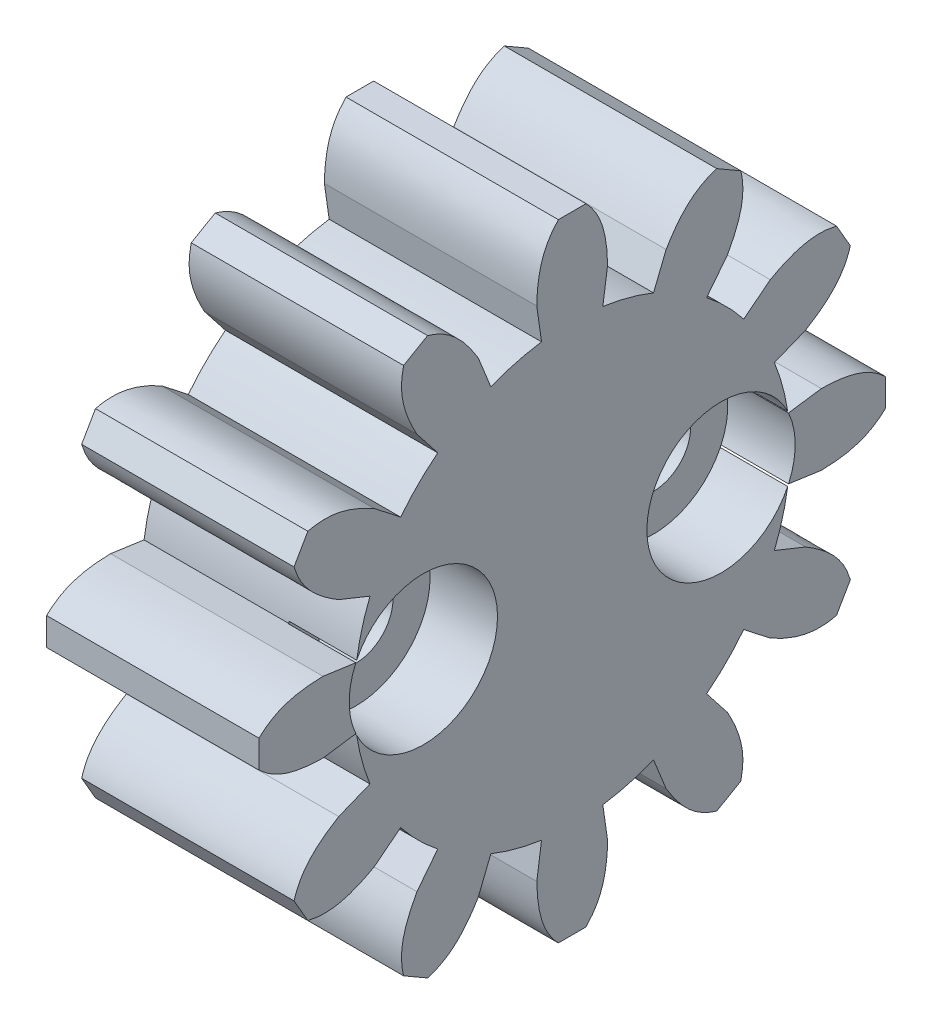
SolidWorks part; units mm, degrees
ref_plane "Front Plane" through (0, 0, 0) normal (0, 0, 1) x (1, 0, 0)
ref_plane "Top Plane" through (0, 0, 0) normal (0, 1, 0) x (1, 0, 0)
ref_plane "Right Plane" through (0, 0, 0) normal (1, 0, 0) x (0, 0, -1)
sketch "Sketch1" plane through (0, 0, 0) normal (1, 0, 0) x (0, 0, -1)
  line L0 (-0.9093, 6.4007) -> (-1.05, 7.3908)
  line L1 (0, 7.3908) -> (0.4109, 7.3908) construction
  line L2 (1.05, 7.3908) -> (0.9093, 6.4007)
  line L3 (1.05, 7.3908) -> (0.4109, 7.3908) construction
  line L4 (0.4109, 7.3908) -> (0.4109, 9.2908) construction
  line L5 (0, 7.3908) -> (0, 7.6117) construction
  line L6 (0.4109, 9.2908) -> (-0.4109, 9.2908)
  line L7 (-0.4109, 7.3908) -> (-0.4109, 9.2908) construction
  line L9 (-1.05, 7.3908) -> (-0.4109, 7.3908) construction
  line L10 (0.4109, 7.3908) -> (1.05, 7.3908) construction
  line L11 (-0.4109, 7.3908) -> (0, 7.3908) construction
  line L12 (4.6047, 5.8756) -> (3.9879, 5.0885)
  line L13 (5.0012, 7.8406) -> (4.2895, 8.2515)
  line L14 (2.4128, 5.9979) -> (2.7861, 6.9256)
  line L15 (6.9256, 2.7861) -> (5.9979, 2.4128)
  line L16 (8.2515, 4.2895) -> (7.8406, 5.0012)
  line L17 (5.0885, 3.9879) -> (5.8756, 4.6047)
  line L18 (7.3908, -1.05) -> (6.4007, -0.9093)
  line L19 (9.2908, -0.4109) -> (9.2908, 0.4109)
  line L20 (6.4007, 0.9093) -> (7.3908, 1.05)
  line L21 (5.8756, -4.6047) -> (5.0885, -3.9879)
  line L22 (7.8406, -5.0012) -> (8.2515, -4.2895)
  line L23 (5.9979, -2.4128) -> (6.9256, -2.7861)
  line L24 (2.7861, -6.9256) -> (2.4128, -5.9979)
  line L25 (4.2895, -8.2515) -> (5.0012, -7.8406)
  line L26 (3.9879, -5.0885) -> (4.6047, -5.8756)
  line L27 (-1.05, -7.3908) -> (-0.9093, -6.4007)
  line L28 (-0.4109, -9.2908) -> (0.4109, -9.2908)
  line L29 (0.9093, -6.4007) -> (1.05, -7.3908)
  line L30 (-4.6047, -5.8756) -> (-3.9879, -5.0885)
  line L31 (-5.0012, -7.8406) -> (-4.2895, -8.2515)
  line L32 (-2.4128, -5.9979) -> (-2.7861, -6.9256)
  line L33 (-6.9256, -2.7861) -> (-5.9979, -2.4128)
  line L34 (-8.2515, -4.2895) -> (-7.8406, -5.0012)
  line L35 (-5.0885, -3.9879) -> (-5.8756, -4.6047)
  line L36 (-7.3908, 1.05) -> (-6.4007, 0.9093)
  line L37 (-9.2908, 0.4109) -> (-9.2908, -0.4109)
  line L38 (-6.4007, -0.9093) -> (-7.3908, -1.05)
  line L39 (-5.8756, 4.6047) -> (-5.0885, 3.9879)
  line L40 (-7.8406, 5.0012) -> (-8.2515, 4.2895)
  line L41 (-5.9979, 2.4128) -> (-6.9256, 2.7861)
  line L42 (-2.7861, 6.9256) -> (-2.4128, 5.9979)
  line L43 (-4.2895, 8.2515) -> (-5.0012, 7.8406)
  line L44 (-3.9879, 5.0885) -> (-4.6047, 5.8756)
  line L45 (0, 0) -> (0.9093, 6.4007) construction
  arc A0 (-0.9093, 6.4007) -> (-2.4128, 5.9979) centre (0, 0) ccw
  arc A2 (-3.9879, 5.0885) -> (-5.0885, 3.9879) centre (0, 0) ccw
  arc A3 (2.4128, 5.9979) -> (0.9093, 6.4007) centre (0, 0) ccw
  arc A4 (-5.9979, 2.4128) -> (-6.4007, 0.9093) centre (0, 0) ccw
  arc A5 (-6.4007, -0.9093) -> (-5.9979, -2.4128) centre (0, 0) ccw
  arc A6 (-5.0885, -3.9879) -> (-3.9879, -5.0885) centre (0, 0) ccw
  arc A7 (-2.4128, -5.9979) -> (-0.9093, -6.4007) centre (0, 0) ccw
  arc A8 (0.9093, -6.4007) -> (2.4128, -5.9979) centre (0, 0) ccw
  arc A9 (3.9879, -5.0885) -> (5.0885, -3.9879) centre (0, 0) ccw
  arc A10 (5.9979, -2.4128) -> (6.4007, -0.9093) centre (0, 0) ccw
  arc A11 (6.4007, 0.9093) -> (5.9979, 2.4128) centre (0, 0) ccw
  arc A12 (5.0885, 3.9879) -> (3.9879, 5.0885) centre (0, 0) ccw
  spline S0 degree 3 poles (0.4109, 9.2908) (0.7612, 8.9159) (1.0342, 8.4403) (1.05, 7.3908) knots 0 0 0 0 1 1 1 1
  spline S1 degree 3 poles (-0.4109, 9.2908) (-0.7612, 8.9159) (-1.0342, 8.4403) (-1.05, 7.3908) knots 0 0 0 0 1 1 1 1
  spline S2 degree 3 poles (5.0012, 7.8406) (5.1172, 7.3408) (5.1158, 6.7924) (4.6047, 5.8756) knots 0 0 0 0 1 1 1 1
  spline S3 degree 3 poles (4.2895, 8.2515) (3.7987, 8.102) (3.3245, 7.8266) (2.7861, 6.9256) knots 0 0 0 0 1 1 1 1
  spline S4 degree 3 poles (8.2515, 4.2895) (8.102, 3.7987) (7.8266, 3.3245) (6.9256, 2.7861) knots 0 0 0 0 1 1 1 1
  spline S5 degree 3 poles (7.8406, 5.0012) (7.3408, 5.1172) (6.7924, 5.1158) (5.8756, 4.6047) knots 0 0 0 0 1 1 1 1
  spline S6 degree 3 poles (9.2908, -0.4109) (8.9159, -0.7612) (8.4403, -1.0342) (7.3908, -1.05) knots 0 0 0 0 1 1 1 1
  spline S7 degree 3 poles (9.2908, 0.4109) (8.9159, 0.7612) (8.4403, 1.0342) (7.3908, 1.05) knots 0 0 0 0 1 1 1 1
  spline S8 degree 3 poles (7.8406, -5.0012) (7.3408, -5.1172) (6.7924, -5.1158) (5.8756, -4.6047) knots 0 0 0 0 1 1 1 1
  spline S9 degree 3 poles (8.2515, -4.2895) (8.102, -3.7987) (7.8266, -3.3245) (6.9256, -2.7861) knots 0 0 0 0 1 1 1 1
  spline S10 degree 3 poles (4.2895, -8.2515) (3.7987, -8.102) (3.3245, -7.8266) (2.7861, -6.9256) knots 0 0 0 0 1 1 1 1
  spline S11 degree 3 poles (5.0012, -7.8406) (5.1172, -7.3408) (5.1158, -6.7924) (4.6047, -5.8756) knots 0 0 0 0 1 1 1 1
  spline S12 degree 3 poles (-0.4109, -9.2908) (-0.7612, -8.9159) (-1.0342, -8.4403) (-1.05, -7.3908) knots 0 0 0 0 1 1 1 1
  spline S13 degree 3 poles (0.4109, -9.2908) (0.7612, -8.9159) (1.0342, -8.4403) (1.05, -7.3908) knots 0 0 0 0 1 1 1 1
  spline S14 degree 3 poles (-5.0012, -7.8406) (-5.1172, -7.3408) (-5.1158, -6.7924) (-4.6047, -5.8756) knots 0 0 0 0 1 1 1 1
  spline S15 degree 3 poles (-4.2895, -8.2515) (-3.7987, -8.102) (-3.3245, -7.8266) (-2.7861, -6.9256) knots 0 0 0 0 1 1 1 1
  spline S16 degree 3 poles (-8.2515, -4.2895) (-8.102, -3.7987) (-7.8266, -3.3245) (-6.9256, -2.7861) knots 0 0 0 0 1 1 1 1
  spline S17 degree 3 poles (-7.8406, -5.0012) (-7.3408, -5.1172) (-6.7924, -5.1158) (-5.8756, -4.6047) knots 0 0 0 0 1 1 1 1
  spline S18 degree 3 poles (-9.2908, 0.4109) (-8.9159, 0.7612) (-8.4403, 1.0342) (-7.3908, 1.05) knots 0 0 0 0 1 1 1 1
  spline S19 degree 3 poles (-9.2908, -0.4109) (-8.9159, -0.7612) (-8.4403, -1.0342) (-7.3908, -1.05) knots 0 0 0 0 1 1 1 1
  spline S20 degree 3 poles (-7.8406, 5.0012) (-7.3408, 5.1172) (-6.7924, 5.1158) (-5.8756, 4.6047) knots 0 0 0 0 1 1 1 1
  spline S21 degree 3 poles (-8.2515, 4.2895) (-8.102, 3.7987) (-7.8266, 3.3245) (-6.9256, 2.7861) knots 0 0 0 0 1 1 1 1
  spline S22 degree 3 poles (-4.2895, 8.2515) (-3.7987, 8.102) (-3.3245, 7.8266) (-2.7861, 6.9256) knots 0 0 0 0 1 1 1 1
  spline S23 degree 3 poles (-5.0012, 7.8406) (-5.1172, 7.3408) (-5.1158, 6.7924) (-4.6047, 5.8756) knots 0 0 0 0 1 1 1 1
  point P14 (0, 9.2908)
  dimension "D2" = 1
  dimension "D3" = 1
  dimension "D4" = 2.1
  dimension "D5" = 1.9
  dimension "D6" = 12
extrude "Boss-Extrude1" add sketch "Sketch1" along normal blind 6.3
sketch "Sketch2" plane through (6.3, 0, 0) normal (1, 0, 0) x (0, 0, -1)
  line L0 (0, 0) -> (4.45, 0) construction
  line L1 (0, 0) -> (0, 1.9305) construction
  circle A1 centre (4.4153, 0) radius 1.1
  circle A2 centre (-4.4153, 0) radius 1.1
  dimension "D2" = 2.2
  dimension "D3" = 4.45
extrude "Cut-Extrude1" cut sketch "Sketch2" against normal through all
sketch "Sketch3" plane through (6.3, 0, 0) normal (1, 0, 0) x (0, 0, -1)
  circle A0 centre (-4.4153, 0) radius 2.2
  circle A1 centre (4.4153, 0) radius 2.2
  dimension "D1" = 4.4
  dimension "D2" = 4.4
extrude "Cut-Extrude2" cut sketch "Sketch3" against normal blind 2
